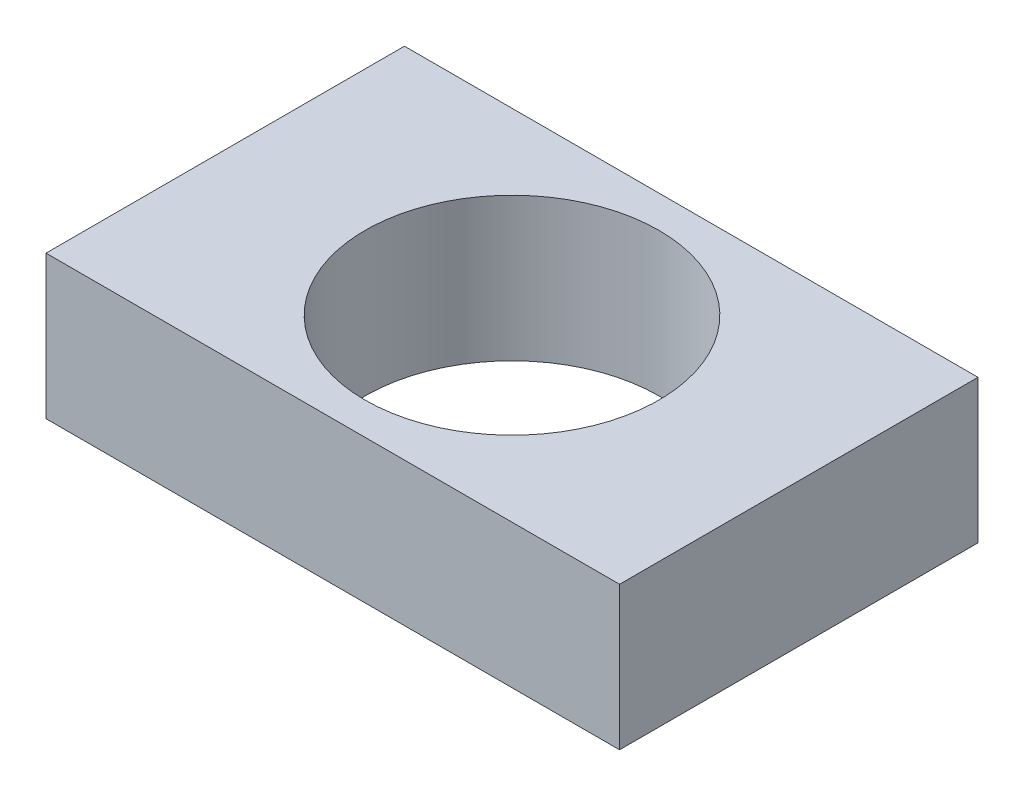
SolidWorks part; units mm, degrees
ref_plane "Front Plane" through (0, 0, 0) normal (0, 0, 1) x (1, 0, 0)
ref_plane "Top Plane" through (0, 0, 0) normal (0, 1, 0) x (1, 0, 0)
ref_plane "Right Plane" through (0, 0, 0) normal (1, 0, 0) x (0, 0, -1)
sketch "Sketch1" plane through (0, 2495.4077, 0) normal (0, 1, 0) x (1, 0, 0)
  line L1 (7.1679, -7.2079) -> (-72.8321, -7.2079)
  line L2 (7.1679, -7.2079) -> (7.1679, 42.7921)
  line L3 (7.1679, 42.7921) -> (-72.8321, 42.7921)
  line L4 (-72.8321, -7.2079) -> (-72.8321, 42.7921)
  line L5 (7.1679, -7.2079) -> (-72.8321, 42.7921) construction
  line L6 (7.1679, 42.7921) -> (-72.8321, -7.2079) construction
  point P0 (-32.8321, 17.7921)
  dimension "D1" = 80
  dimension "D2" = 50
extrude "Boss-Extrude1" add sketch "Sketch1" along normal blind 20
sketch "Sketch2" plane through (0, 2495.4077, 0) normal (0, -1, 0) x (1, 0, 0)
  circle A0 centre (-32.8321, -17.7921) radius 20.5
  dimension "D1" = 41
extrude "Cut-Extrude1" cut sketch "Sketch2" against normal up to next
